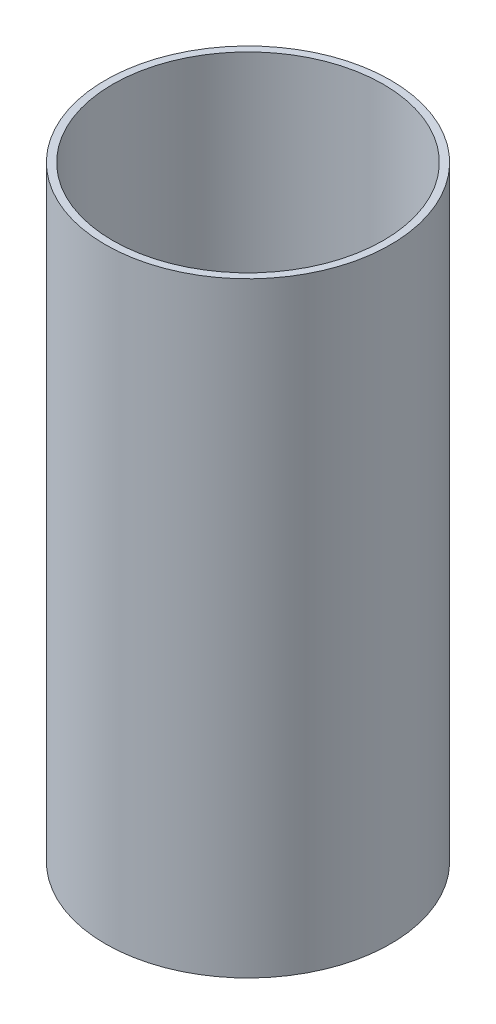
SolidWorks part; units mm, degrees
material "PVC Rigid"
ref_plane "Front Plane" through (0, 0, 0) normal (0, 0, 1) x (1, 0, 0)
ref_plane "Top Plane" through (0, 0, 0) normal (0, 1, 0) x (1, 0, 0)
ref_plane "Right Plane" through (0, 0, 0) normal (1, 0, 0) x (0, 0, -1)
sketch "Sketch1" plane through (0, 0, 0) normal (0, 1, 0) x (1, 0, 0)
  circle A0 centre (0, 0) radius 93.6625
  circle A1 centre (0, 0) radius 88.9
  dimension "D1" = 187.325
  dimension "D2" = 177.8
extrude "Boss-Extrude1" add sketch "Sketch1" along normal mid plane 397.764
